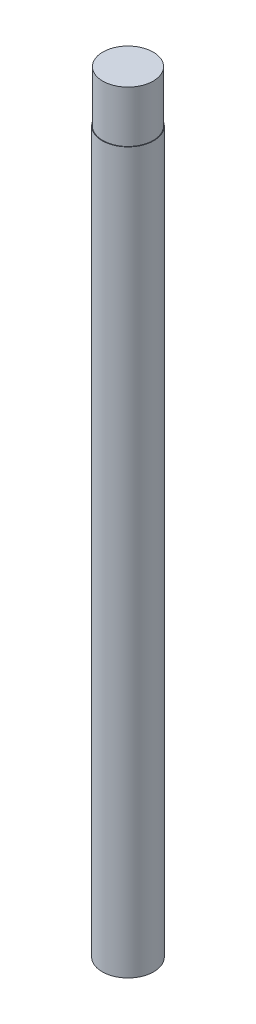
SolidWorks part; units mm, degrees
ref_plane "Front Plane" through (0, 0, 0) normal (0, 0, 1) x (1, 0, 0)
ref_plane "Top Plane" through (0, 0, 0) normal (0, 1, 0) x (1, 0, 0)
ref_plane "Right Plane" through (0, 0, 0) normal (1, 0, 0) x (0, 0, -1)
sketch "Sketch1" plane through (0, 0, 0) normal (0, 1, 0) x (1, 0, 0)
  circle A0 centre (0, 0) radius 5
  dimension "D1" = 10
extrude "Boss-Extrude1" add sketch "Sketch1" along normal blind 150
sketch "Sketch2" plane through (0, 150, 0) normal (0, 1, 0) x (1, 0, 0)
  circle A0 centre (0, 0) radius 4.9
  circle A1 centre (0, 0) radius 5
  dimension "D1" = 9.8
extrude "Cut-Extrude1" cut sketch "Sketch2" against normal blind 10
